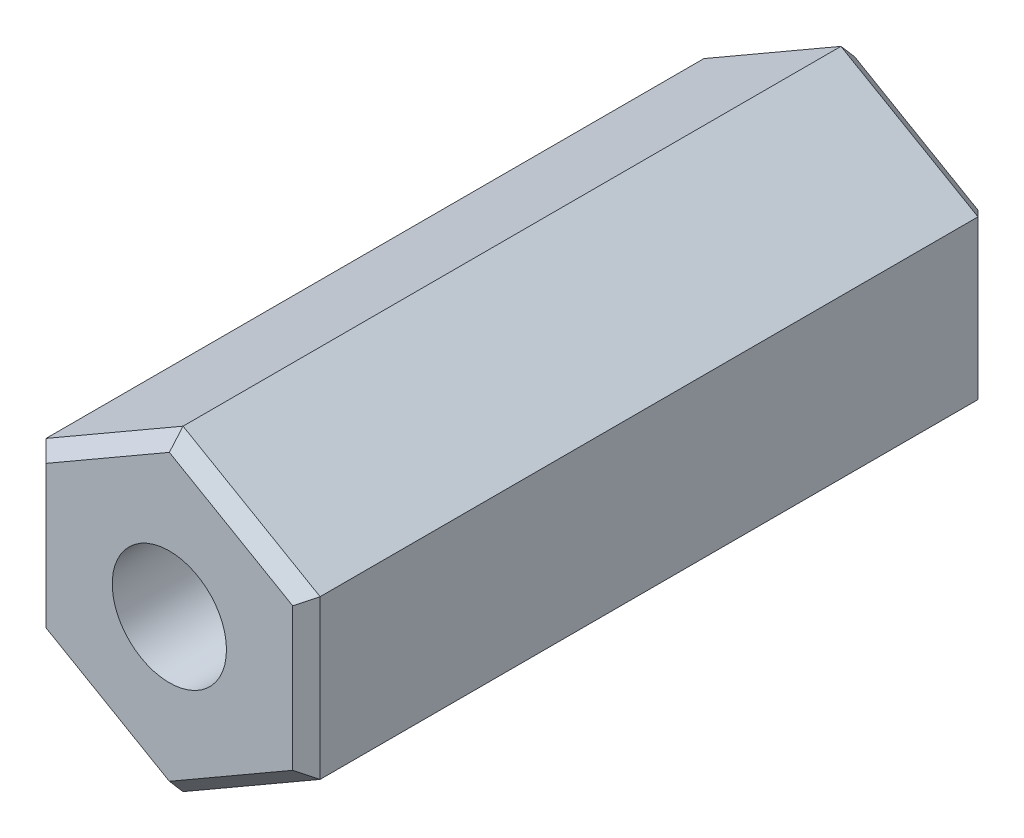
SolidWorks part; units mm, degrees
material "3003 Alloy"
ref_plane "Ebene vorne" through (0, 0, 0) normal (0, 0, 1) x (1, 0, 0)
ref_plane "Ebene oben" through (0, 0, 0) normal (0, 1, 0) x (1, 0, 0)
ref_plane "Ebene rechts" through (0, 0, 0) normal (1, 0, 0) x (0, 0, -1)
sketch "Sketch1" plane through (0, 0, 0) normal (0, 0, 1) x (1, 0, 0)
  line L1 (0, 3.4641) -> (-3, 1.7321)
  line L2 (-3, 1.7321) -> (-3, -1.7321)
  line L3 (-3, -1.7321) -> (0, -3.4641)
  line L4 (0, -3.4641) -> (3, -1.7321)
  line L5 (3, -1.7321) -> (3, 1.7321)
  line L6 (3, 1.7321) -> (0, 3.4641)
  circle A0 centre (0, 0) radius 3 construction
  dimension "D1" = 6
extrude "Boss-Extrude1" add sketch "Sketch1" along normal blind 15
hole_wizard "M3 Tapped Hole1" positions "Sketch3" profile "Sketch4" tap size "M3" standard "DIN"
sketch "Sketch3" plane through (0, 0, 15) normal (0, 0, 1) x (1, 0, 0)
  point P0 (0, 0)
sketch "Sketch4" plane through (0, 0, 15) normal (1, 0, 0) x (0, -1, 0)
  line L0 (0, 0) -> (0, 6.7511)
  line L1 (0, 6.7511) -> (1.25, 6)
  line L2 (1.25, 6) -> (1.25, 0)
  line L5 (1.25, 0) -> (0, 0)
  line L10 (0, 6.7511) -> (-1.25, 6) construction
  line L11 (0, -6.35) -> (0, 107.95) construction
  dimension "Tap Drill Dia." = 2.5
  dimension "Tap Drill Depth" = 6
  dimension "Drill Angle" = 118
cosmetic thread "Hole Thread1" parameters "D1"=6, "D2"=3
hole_wizard "M3 Tapped Hole2" positions "Sketch6" profile "Sketch5" tap size "M3" standard "DIN"
sketch "Sketch6" plane through (0, 0, 0) normal (0, 0, -1) x (-1, 0, 0)
  point P0 (0, 0)
sketch "Sketch5" plane through (0, 0, 0) normal (1, 0, 0) x (0, 1, 0)
  line L0 (0, 0) -> (0, 7.7511)
  line L1 (0, 7.7511) -> (1.25, 7)
  line L2 (1.25, 7) -> (1.25, 0)
  line L5 (1.25, 0) -> (0, 0)
  line L10 (0, 7.7511) -> (-1.25, 7) construction
  line L11 (0, -6.35) -> (0, 107.95) construction
  dimension "Tap Drill Dia." = 2.5
  dimension "Tap Drill Depth" = 7
  dimension "Drill Angle" = 118
cosmetic thread "Hole Thread2" parameters "D1"=5.5, "D2"=3
chamfer "Chamfer1" distance 0.3 angle 45 12 edges at (-3, 0, 0) (-1.5, -2.5981, 0) (1.5, -2.5981, 0) (3, 0, 0) (1.5, 2.5981, 0) (-1.5, 2.5981, 0) (3, 0, 15) (1.5, -2.5981, 15) (-1.5, -2.5981, 15) (-3, 0, 15) (-1.5, 2.5981, 15) (1.5, 2.5981, 15)
